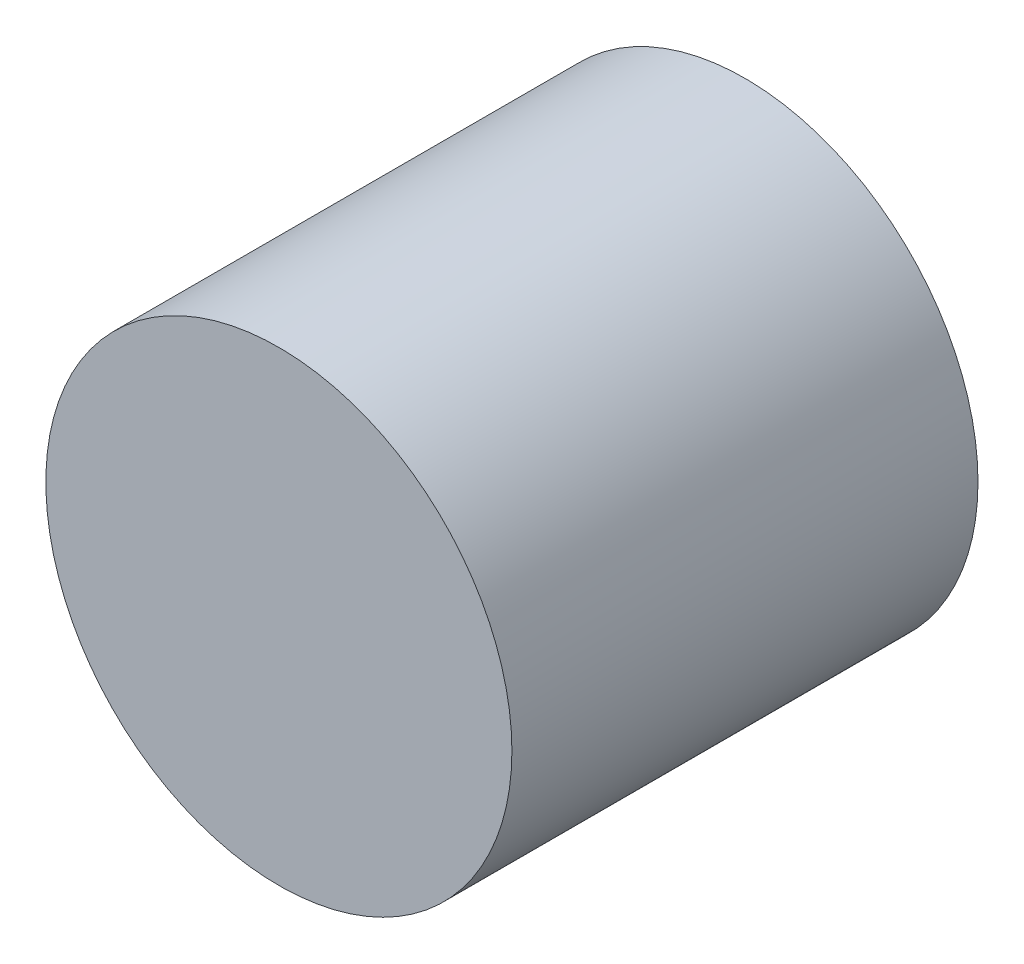
SolidWorks part; units mm, degrees
ref_plane "Front Plane" through (0, 0, 0) normal (0, 0, 1) x (1, 0, 0)
ref_plane "Top Plane" through (0, 0, 0) normal (0, 1, 0) x (1, 0, 0)
ref_plane "Right Plane" through (0, 0, 0) normal (1, 0, 0) x (0, 0, -1)
sketch "Sketch1" plane through (0, 0, 0) normal (0, 0, 1) x (1, 0, 0)
  circle A0 centre (0, 0) radius 2.5
extrude "Boss-Extrude1" add sketch "Sketch1" along normal blind 5
